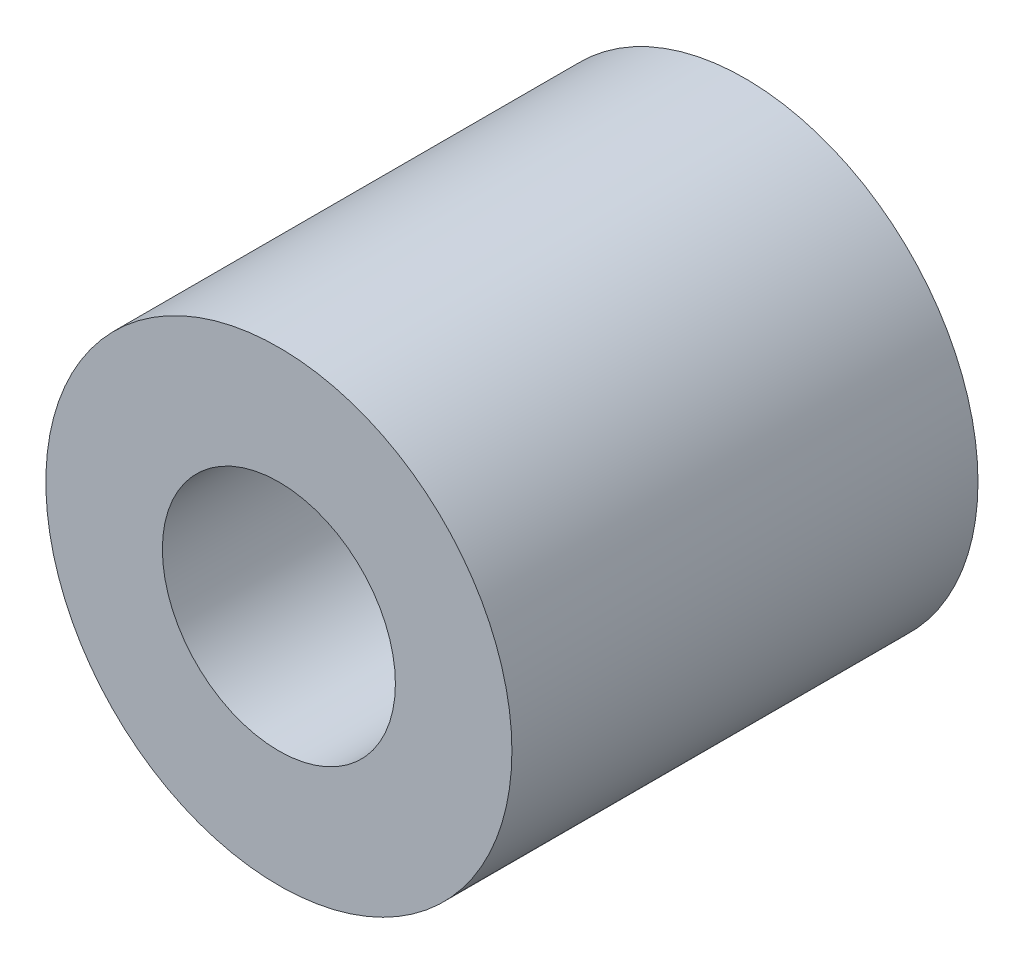
SolidWorks part; units mm, degrees
ref_plane "前视基准面" through (0, 0, 0) normal (0, 0, 1) x (1, 0, 0)
ref_plane "上视基准面" through (0, 0, 0) normal (0, 1, 0) x (1, 0, 0)
ref_plane "右视基准面" through (0, 0, 0) normal (1, 0, 0) x (0, 0, -1)
sketch "草图1" plane through (0, 0, 0) normal (0, 0, 1) x (1, 0, 0)
  circle A0 centre (0, 0) radius 4
  dimension "D1" = 8
extrude "凸台-拉伸1" add sketch "草图1" along normal blind 8
sketch "草图2" plane through (0, 0, 8) normal (0, 0, 1) x (1, 0, 0)
  circle A0 centre (0, 0) radius 2
  dimension "D1" = 4
extrude "切除-拉伸1" cut sketch "草图2" against normal blind 15
